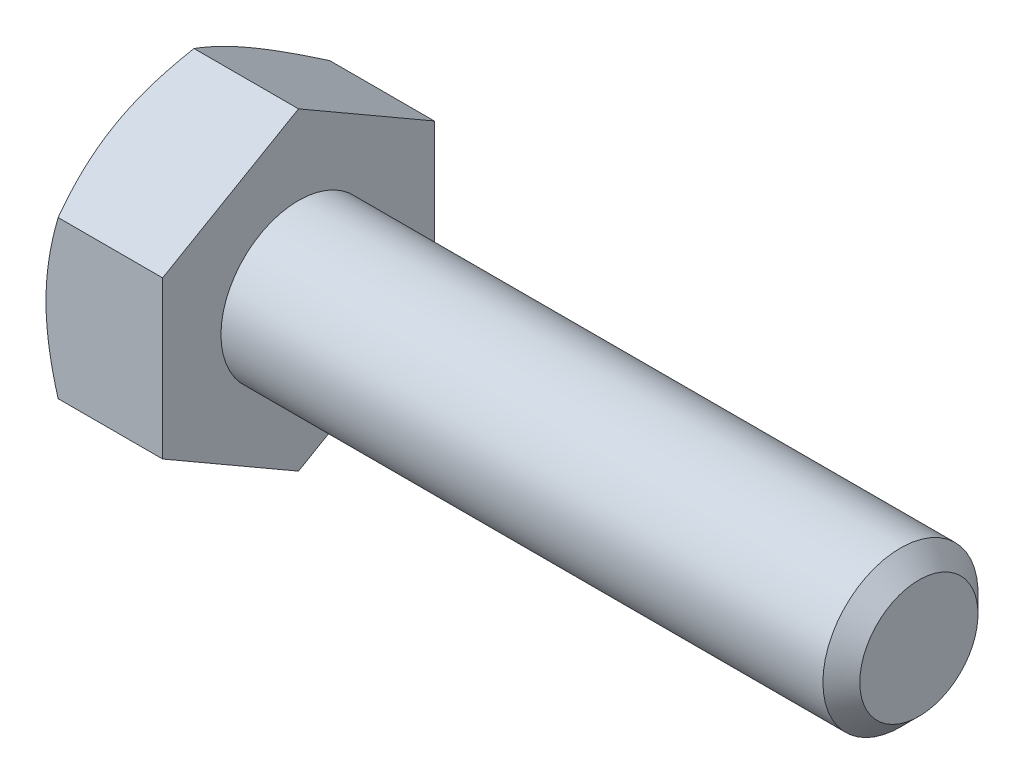
SolidWorks part; units mm, degrees
extrude "BaseHead" add sketch "Sketch1" along normal blind 4.7752
sketch "Sketch1" plane through (0, 0, 0) normal (1, 0, 0) x (0, 0, -1)
  line L0 (5.5626, 3.2116) -> (5.5626, -3.2116)
  line L1 (-5.5626, 3.2116) -> (-5.5626, -3.2116)
  line L2 (5.5626, -3.2116) -> (0, -6.4231)
  line L3 (0, -6.4231) -> (-5.5626, -3.2116)
  line L4 (5.5626, 3.2116) -> (0, 6.4231)
  line L5 (0, 6.4231) -> (-5.5626, 3.2116)
  dimension "Width_flats" = 11.1252
  dimension "D2" = 120
  dimension "D3" = 5.5626
  dimension "D4" = 5.5626
  dimension "D5" = 5.5626
material "1023 Carbon Steel Sheet (SS)"
ref_plane "Plane1" through (0, 0, 0) normal (0, 0, 1) x (1, 0, 0)
ref_plane "Plane2" through (0, 0, 0) normal (0, 1, 0) x (1, 0, 0)
ref_plane "Plane3" through (0, 0, 0) normal (1, 0, 0) x (0, 0, -1)
sketch "BodySke" plane through (0, 0, 0) normal (0, 0, 1) x (1, 0, 0)
  line L0 (0, 3.2116) -> (0, -3.2116) construction
  line L1 (0, 0) -> (30.1752, 0)
  line L2 (0, 0) -> (0, 3.175)
  line L3 (0, 3.175) -> (29.4195, 3.175)
  line L4 (30.1752, 0) -> (30.1752, 2.4193)
  line L5 (4.7752, 6.4231) -> (4.7752, 3.2116) construction
  line L6 (30.1752, 2.4193) -> (29.4195, 3.175)
  line L7 (0, 0) -> (96.52, 0) construction
  line L8 (30.1752, -2.4193) -> (29.4195, -3.175) construction
  line L9 (0, -3.175) -> (29.4195, -3.175) construction
  line L10 (6.0452, 15.24) -> (6.0452, -2.54) construction
  line L11 (4.7752, 15.24) -> (4.7752, -2.54) construction
  line L12 (4.7752, 3.2116) -> (4.7752, -3.2116) construction
  dimension "Diameter" = 6.35
  dimension "Advance" = 1.27
revolve "BaseBody" add sketch "BodySke" angle 360 about L7
cosmetic thread "ThreadCosmetic"
sketch "Sketch3" plane through (0, 0, 0) normal (0, 0, 1) x (1, 0, 0)
  line L0 (0, 5.5626) -> (4.163, 12.7731)
  line L1 (0, 6.4231) -> (0, 3.2116) construction
  line L2 (4.163, 12.7731) -> (4.163, 19.1231)
  line L3 (4.163, 19.1231) -> (-12.7, 19.1231)
  line L4 (-12.7, 19.1231) -> (-12.7, 5.5626)
  line L5 (-12.7, 5.5626) -> (0, 5.5626)
  line L6 (0, 0) -> (99.06, 0) construction
  line L7 (4.7752, 6.4231) -> (0, 6.4231) construction
  dimension "D1" = 5.5626
  dimension "D2" = 6.35
  dimension "D3" = 12.7
  dimension "D4" = 6.35
  dimension "Head_ch_ang" = 30
revolve "HeadChamfer" cut sketch "Sketch3" angle 360 about L6
fillet "HeadFillet" [suppressed] radius 0.762
sketch "ThdSchSke" plane through (0, 0, 0) normal (0, 0, 1) x (1, 0, 0)
  line L0 (6.0452, -2.4194) -> (5.5161, -3.175)
  line L1 (6.0452, -2.4194) -> (6.5743, -3.175)
  line L2 (6.5743, -3.175) -> (6.5743, -3.9688)
  line L3 (-3.175, 0) -> (5.1513, 0) construction
  line L5 (6.5743, -3.9688) -> (5.5161, -3.9688)
  line L6 (5.5161, -3.9688) -> (5.5161, -3.175)
  dimension "Thread_minor" = 4.8387
  dimension "Diameter" = 6.35
  dimension "Start" = 6.0452
revolve "ThreadSchematic" [suppressed] cut sketch "ThdSchSke" angle 360 about L3
pattern_linear "ThdSchPat" [suppressed]
equation "\"D3@Sketch1\" = \"Width_flats@Sketch1\" / 2"
equation "\"D4@Sketch1\" = \"D3@Sketch1\""
equation "\"D5@Sketch1\" = \"D4@Sketch1\""
equation "\"Thread_minor@ThreadCosmetic\" = \"Minor_dia@BodySke\""
equation "\"D1@Sketch3\" = \"Width_flats@Sketch1\" / 2"
equation "\"Thread_length@ThreadCosmetic\" = ((sgn( (\"Length@BodySke\" - \"Advance@BodySke\" ) - \"Thread_nom@BodySke\" )-1)*( (\"Length@BodySke\" - \"Advance@BodySke\" ) - \"Thread_nom@BodySke\" ))/-2+ \"Thread_nom@BodySke\""
equation "\"Thread_minor@ThdSchSke\" = \"Minor_dia@BodySke\""
equation "\"Diameter@ThdSchSke\" = \"Diameter@BodySke\""
equation "\"Overcut@ThdSchSke\" = \"Diameter@BodySke\" * 1.25"
equation "\"Start@ThdSchSke\" = \"Head_ht@BaseHead\" + \"Length@BodySke\" - \"Thread_length@ThreadCosmetic\"  '---Non-countersunk---"
equation "\"Num_threads@ThdSchPat\" = int( \"Thread_length@ThreadCosmetic\" / \"Advance@BodySke\" + 0.999 )  + 1"
equation "\"Advance@ThdSchPat\" = \"Thread_length@ThreadCosmetic\" /  (\"Num_threads@ThdSchPat\" - 1) 'relax it"
equation "\"Num_threads@ThdSchPat\" = \"Num_threads@ThdSchPat\" - sgn( \"Num_threads@ThdSchPat\" - 1) '---chamfered tips only---"
